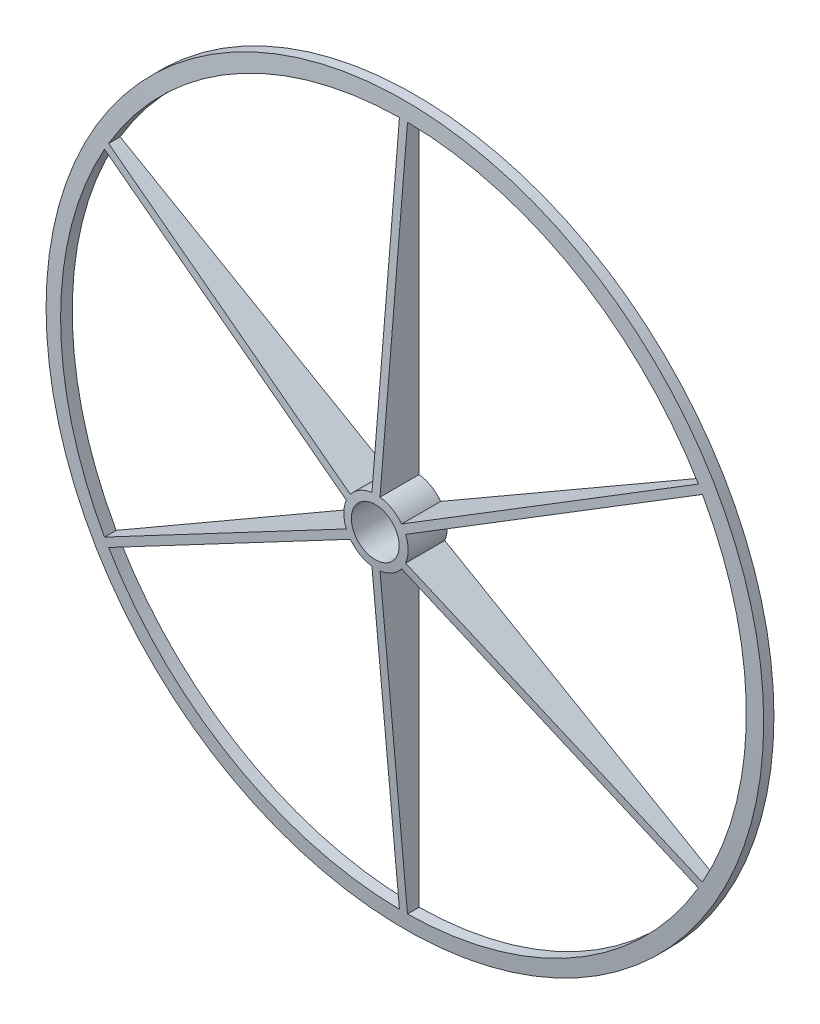
SolidWorks part; units mm, degrees
ref_plane "Front Plane" through (0, 0, 0) normal (0, 0, 1) x (1, 0, 0)
ref_plane "Top Plane" through (0, 0, 0) normal (0, 1, 0) x (1, 0, 0)
ref_plane "Right Plane" through (0, 0, 0) normal (1, 0, 0) x (0, 0, -1)
sketch "Sketch1" plane through (0, 0, 0) normal (0, 1, 0) x (1, 0, 0)
  line L0 (0, 27.7159) -> (0, -35.7841)
  line L1 (0, -35.7841) -> (-533.4, 11.43)
  line L2 (-533.4, 11.43) -> (-533.4, 27.7159)
  line L3 (-533.4, 27.7159) -> (0, 27.7159)
  line L4 (38.1, 15.0159) -> (38.1, -23.0841) construction
  dimension "D1" = 63.5
  dimension "D2" = 38.1
  dimension "D3" = 533.4
revolve "Revolve1" add sketch "Sketch1" angle 360 about L4
sketch "Sketch2" plane through (0, 0, -27.7159) normal (0, 0, -1) x (-1, 0, 0)
  line L1 (-31.6753, 50.8) -> (-31.6753, 1079.5)
  line L2 (-44.5247, 50.8) -> (-44.5247, 1079.5)
  line L3 (-85.3064, 19.836) -> (-976.1868, 534.186)
  line L4 (-78.8817, 30.964) -> (-969.7621, 545.314)
  line L5 (-78.8817, -30.964) -> (-969.7621, -545.314)
  line L6 (-85.3064, -19.836) -> (-976.1868, -534.186)
  line L7 (-31.6753, -50.8) -> (-31.6753, -1079.5)
  line L8 (-44.5247, -50.8) -> (-44.5247, -1079.5)
  line L9 (9.1064, -19.836) -> (899.9868, -534.186)
  line L10 (2.6817, -30.964) -> (893.5621, -545.314)
  line L11 (2.6817, 30.964) -> (893.5621, 545.314)
  line L12 (9.1064, 19.836) -> (899.9868, 534.186)
  arc A0 (-31.6753, -546.0622) -> (431.5914, -278.5951) centre (-38.1, 0) ccw
  circle A1 centre (-38.1, 0) radius 571.5 construction
  arc A2 (-85.3064, 19.836) -> (-85.3064, -19.836) centre (-38.1, 0) ccw
  arc A3 (-31.6753, -1079.5) -> (893.5621, -545.314) centre (-38.1, 0) ccw
  arc A4 (899.9868, -534.186) -> (899.9868, 534.186) centre (-38.1, 0) ccw
  arc A5 (438.0161, -267.4671) -> (438.0161, 267.4671) centre (-38.1, 0) ccw
  arc A6 (893.5621, 545.314) -> (-31.6753, 1079.5) centre (-38.1, 0) ccw
  arc A7 (431.5914, 278.5951) -> (-31.6753, 546.0622) centre (-38.1, 0) ccw
  arc A8 (-44.5247, 1079.5) -> (-969.7621, 545.314) centre (-38.1, 0) ccw
  arc A9 (-44.5247, 546.0622) -> (-507.7914, 278.5951) centre (-38.1, 0) ccw
  arc A10 (-976.1868, 534.186) -> (-976.1868, -534.186) centre (-38.1, 0) ccw
  arc A11 (-514.2161, 267.4671) -> (-514.2161, -267.4671) centre (-38.1, 0) ccw
  arc A12 (-969.7621, -545.314) -> (-44.5247, -1079.5) centre (-38.1, 0) ccw
  arc A13 (-507.7914, -278.5951) -> (-44.5247, -546.0622) centre (-38.1, 0) ccw
  arc A14 (-44.5247, 50.8) -> (-78.8817, 30.964) centre (-38.1, 0) ccw
  arc A15 (2.6817, 30.964) -> (-31.6753, 50.8) centre (-38.1, 0) ccw
  arc A16 (9.1064, -19.836) -> (9.1064, 19.836) centre (-38.1, 0) ccw
  arc A17 (-31.6753, -50.8) -> (2.6817, -30.964) centre (-38.1, 0) ccw
  arc A18 (-78.8817, -30.964) -> (-44.5247, -50.8) centre (-38.1, 0) ccw
  point P35 (-38.1, 0)
  dimension "D1" = 25.4
  dimension "D4" = 6
extrude "Cut-Extrude1" cut sketch "Sketch2" against normal blind 127 contours L3 A11 L6 A2 | A14 L2 A9 L4 | A15 L11 A7 L1 | A16 L9 A5 L12 | A17 L7 A0 L10 | A18 L5 A13 L8
sketch "Sketch3" plane through (0, 0, 0) normal (0, 0, 1) x (1, 0, 0)
  circle A0 centre (982.9631, 544.767) radius 6.35
  circle A1 centre (963.2636, -578.8875) radius 6.35
  circle A2 centre (-19.6994, -1123.6545) radius 6.35
  circle A3 centre (-982.9631, -544.767) radius 6.35
  circle A4 centre (-963.2636, 578.8875) radius 6.35
  circle A5 centre (19.6994, 1123.6545) radius 6.35
  point P15 (0, 0)
  dimension "D1" = 12.7
  dimension "D2" = 6
extrude "Cut-Extrude2" cut sketch "Sketch3" against normal blind 127
